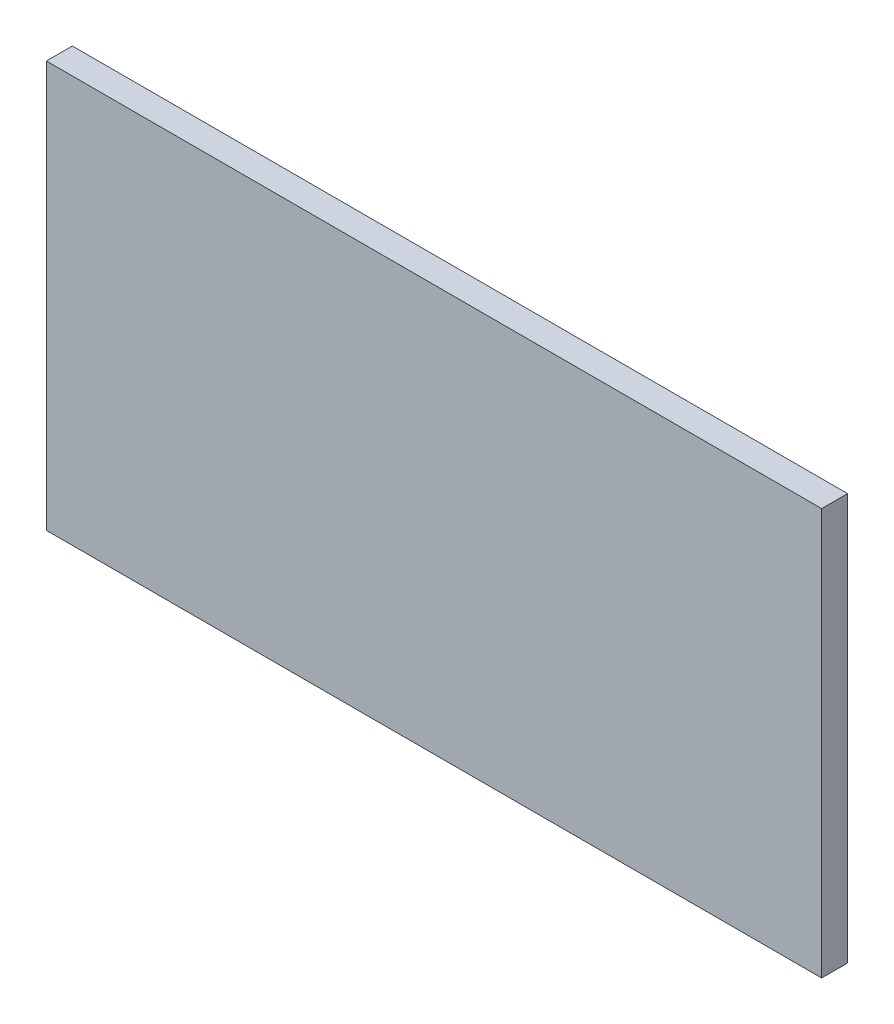
SolidWorks part; units mm, degrees
ref_plane "Front Plane" through (0, 0, 0) normal (0, 0, 1) x (1, 0, 0)
ref_plane "Top Plane" through (0, 0, 0) normal (0, 1, 0) x (1, 0, 0)
ref_plane "Right Plane" through (0, 0, 0) normal (1, 0, 0) x (0, 0, -1)
sketch "Sketch2" plane through (0, 0, 0) normal (0, 1, 0) x (1, 0, 0)
  line L0 (0, 0) -> (0, 6) construction
  point P3 (0, 0)
  dimension "D1" = 6
sketch "Sketch1" plane through (0, 0, 0) normal (0, 0, 1) x (1, 0, 0)
  line L1 (-89.6354, -46.9996) -> (89.6354, -46.9996)
  line L2 (-89.6354, -46.9996) -> (-89.6354, 46.9996)
  line L3 (-89.6354, 46.9996) -> (89.6354, 46.9996)
  line L4 (89.6354, -46.9996) -> (89.6354, 46.9996)
  line L5 (-89.6354, -46.9996) -> (89.6354, 46.9996) construction
  line L6 (-89.6354, 46.9996) -> (89.6354, -46.9996) construction
  point P0 (0, 0)
extrude "Boss-Extrude1" add sketch "Sketch1" against normal up to vertex (6 mm away) contours L2 L3 L4 L1 up to point (0, 0, -6)
equation "\"t_wood\"= 6' Thickness of the wood"
equation "\"t_glass\"= 2.5'Thickness of glass panels"
equation "\"w_glass\"= 151"
equation "\"h_glass\"= 181"
equation "\"h_food_internal\" = 60"
equation "\"entry_height\"= 20"
equation "\"entry diameter\"= 8"
equation "\"glass_bottom_overlap\"= 8"
equation "\"default_finger_size\"= 12"
equation "\"brood_depth\"= 42"
equation "\"outer_box_depth\" = \"brood_depth\" + ( 2 * \"t_glass\" ) + ( 2 * \"t_wood\" )"
equation "\"outer_box_width\"= \"w_glass\" + ( 2 * \"t_wood\" )"
equation "\"food_top_clearance\"= 10"
equation "\"outer_box_height\"= \"t_wood\" + \"h_glass\" + \"t_wood\" + \"h_food_internal\" + \"food_top_clearance\" + \"t_wood\""
equation "\"food_internal_depth\"= \"brood_depth\" + \"t_glass\" + \"t_glass\" - \"t_wood\" - \"t_wood\""
equation "\"food_channel_clearance_width\"= 10"
equation "\"bar_top_play\"= 0.5"
equation "\"bar_entry_angle\"= 10"
equation "\"bar_width\"= 20"
equation "\"entry_disk_play\"= 0.5"
equation "\"D1@Sketch2\"=\"t_wood\""
